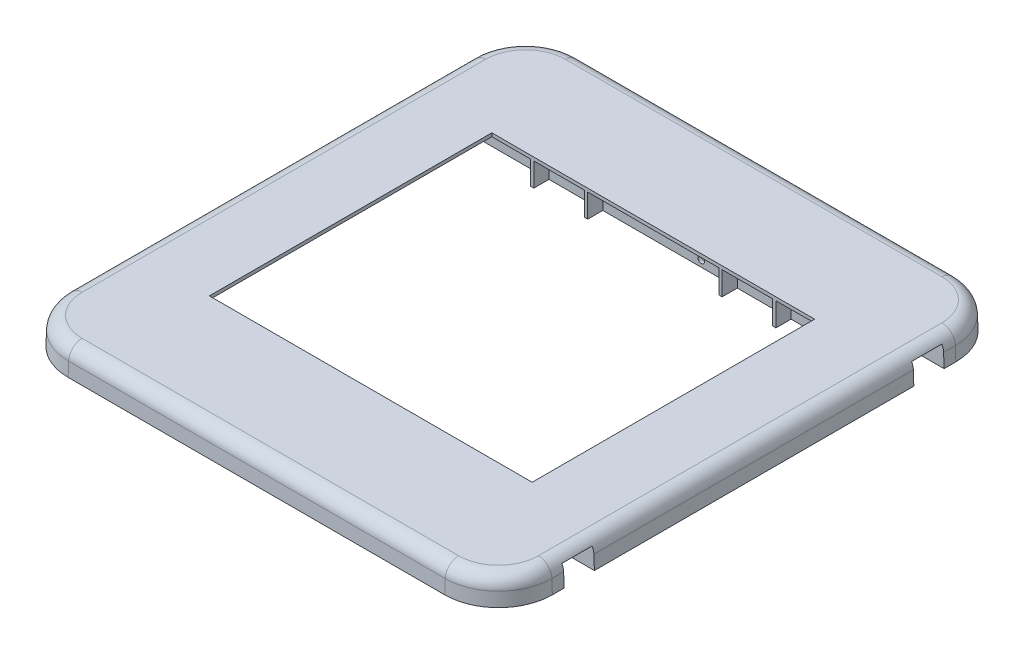
SolidWorks part; units mm, degrees
material "ABS PC"
ref_plane "Front Plane" through (0, 0, 0) normal (0, 0, 1) x (1, 0, 0)
ref_plane "Top Plane" through (0, 0, 0) normal (0, 1, 0) x (1, 0, 0)
ref_plane "Right Plane" through (0, 0, 0) normal (1, 0, 0) x (0, 0, -1)
sketch "Sketch1" plane through (0, 0, 0) normal (0, 1, 0) x (1, 0, 0)
  line L1 (-228.6, 0) -> (-256.2277, 0) construction
  line L2 (228.6, 0) -> (228.6, 190.5)
  line L3 (177.8, 241.3) -> (-177.8, 241.3)
  line L4 (-228.6, 0) -> (-228.6, 190.5)
  line L5 (-228.6, 0) -> (228.6, 0)
  arc A0 (-177.8, 241.3) -> (-228.6, 190.5) centre (-177.8, 190.5) ccw
  arc A1 (228.6, 190.5) -> (177.8, 241.3) centre (177.8, 190.5) ccw
  dimension "D3" = 50.8
  dimension "D1" = 457.2
  dimension "D2" = 482.6
extrude "Extrude1" add sketch "Sketch1" along normal blind 25.4
draft "Draft1" type of draft neutral plane draft angle 2 faces to draft 1 face at (228.6, 12.7, -95.25) neutral plane through (-177.8, 0, -190.5) neutral plane normal (0, -1, 0) reverse direction yes parameters "D1"=2
fillet "Fillet1" radius 12.7 5 edges at (-227.713, 25.4, -95.25) (-213.0938, 25.4, -225.7938) (0, 25.4, -240.413) (213.0938, 25.4, -225.7938) (227.713, 25.4, -95.25)
shell "Shell2" thickness 3.175
sketch "Sketch3" plane through (0, 0, 0) normal (0, -1, 0) x (1, 0, 0)
  line L1 (-225.4231, -190.5) -> (-225.4231, 0) construction
  line L4 (-225.4231, -149.225) -> (215.4488, -149.225)
  line L5 (215.4488, 0) -> (215.4488, -190.5) construction
  line L6 (-228.6, -180.975) -> (215.4488, -180.975)
  line L7 (-228.6, -190.5) -> (-228.6, 0) construction
  line L8 (0, 0) -> (223.0829, 0) construction
  dimension "D1" = 298.45
  dimension "D2" = 361.95
rib "Rib1" sketch "Sketch3" sketch "Sketch3" thickness 3.175 extrusion direction normal to sketch draft on no parameters "D1"=3.175
sketch "Sketch4" plane through (0, 0, 0) normal (1, 0, 0) x (0, 0, -1)
  line L0 (150.8125, 19.05) -> (179.3875, 19.05)
  line L1 (150.8125, 19.05) -> (179.3875, 19.05) construction
  line L2 (150.8125, 0) -> (179.3875, 0) construction
  line L3 (150.8125, 22.225) -> (179.3875, 22.225) construction
  line L4 (150.8125, 13.0324) -> (150.8125, 0) construction
  line L5 (179.3875, 13.0324) -> (179.3875, 0) construction
  line L6 (150.8125, 0) -> (179.3875, 0)
  line L7 (150.8125, 22.225) -> (179.3875, 22.225) construction
  line L8 (150.8125, 0) -> (150.8125, 19.05)
  line L9 (179.3875, 0) -> (179.3875, 19.05)
  dimension "D1" = 3.175
extrude "Cut-Extrude2" cut sketch "Sketch4" along normal through all
sketch "Sketch6" plane through (0, 0, 0) normal (0, 0, 1) x (1, 0, 0)
  line L0 (228.141, 13.1432) -> (228.6, 0) construction
  line L1 (-225.4231, 0) -> (225.4231, 0) construction
  circle A1 centre (208.9354, 6.35) radius 3.175
  circle A3 centre (31.1354, 6.35) radius 3.175
  dimension "D2" = 6.35
  dimension "D3" = 177.8
  dimension "D4" = 19.431
  dimension "D1" = 6.35
extrude "Cut-Extrude3" cut sketch "Sketch6" against normal up to surface (207.9625 mm away) from offset 25.4
sketch "Sketch9" plane through (0, 19.05, 0) normal (0, -1, 0) x (1, 0, 0)
  line L0 (0, 0) -> (0, -59.2425) construction
  line L1 (63.5, -150.8125) -> (63.5, -179.3875)
  line L2 (-225.4231, -150.8125) -> (228.6, -150.8125) construction
  line L3 (-225.4231, -179.3875) -> (228.6, -179.3875) construction
  line L4 (-63.5, -150.8125) -> (-63.5, -179.3875)
  dimension "D1" = 127
rib "Rib4" sketch "Sketch9" sketch "Sketch9" thickness 3.175 extrusion direction normal to sketch draft on yes draft angle 2 parameters "D1"=3.175, "D3"=2
mirror "Mirror1" about plane through (-228.6, 25.4, 0) normal (0, 0, -1) of bodies 105 107
sketch "Sketch11" plane through (0, 0, 0) normal (0, -1, 0) x (1, 0, 0)
  line L0 (63.5, 147.6375) -> (63.5, -147.6375)
  line L5 (-225.4231, 147.6375) -> (225.4231, 147.6375) construction
  line L6 (-225.4231, -147.6375) -> (225.4231, -147.6375) construction
  line L7 (-63.5, 147.6375) -> (-63.5, -150.8125)
  line L8 (-225.4231, -150.8125) -> (228.6, -150.8125) construction
  line L9 (-63.5, -150.8125) -> (-63.5, -179.3875) construction
  line L10 (63.5, -150.8125) -> (63.5, -179.3875) construction
  line L11 (114.3, 147.6375) -> (114.3, -147.6375)
  line L12 (-114.3, 147.6375) -> (-114.3, -150.8125)
  dimension "D1" = 50.8
  dimension "D2" = 50.8
rib "Rib5" sketch "Sketch11" sketch "Sketch11" thickness 3.175 extrusion direction normal to sketch draft on no parameters "D1"=3.175
sketch "Sketch10" plane through (0, 25.4, 0) normal (0, 1, 0) x (-1, 0, 0)
  line L1 (152.4, 0) -> (-152.4, 0) construction
  line L2 (152.4, 133.35) -> (152.4, -133.35)
  line L3 (152.4, -133.35) -> (-152.4, -133.35)
  line L4 (-152.4, 133.35) -> (-152.4, -133.35)
  line L5 (152.4, 133.35) -> (-152.4, 133.35)
  dimension "D1" = 304.8
  dimension "D2" = 266.7
extrude "Cut-Extrude4" cut sketch "Sketch10" against normal through all
